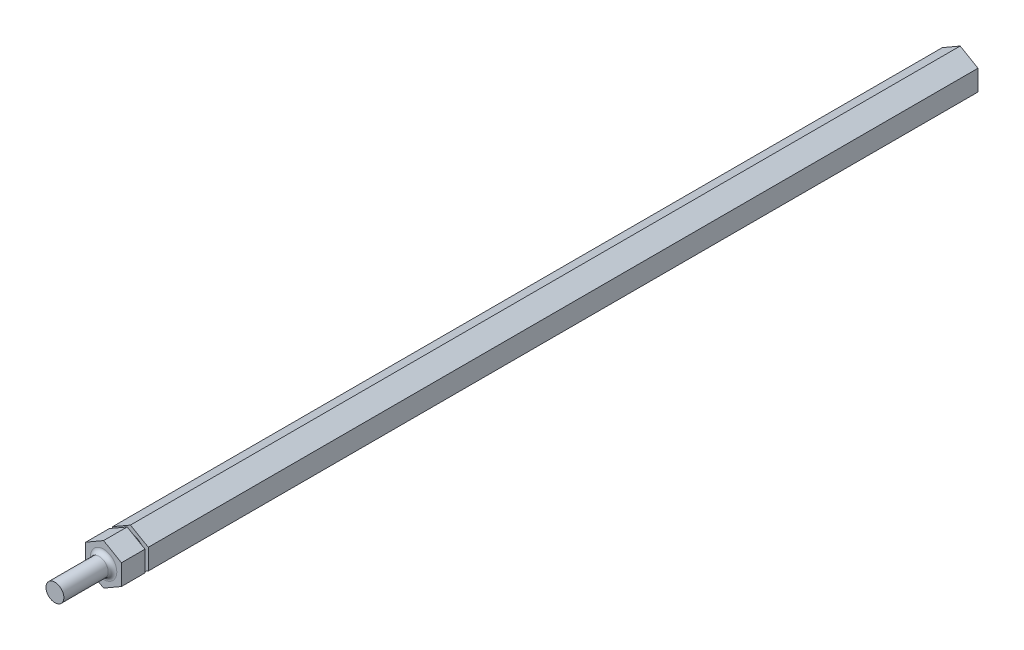
SolidWorks part; units mm, degrees
ref_plane "Front Plane" through (0, 0, 0) normal (0, 0, 1) x (1, 0, 0)
ref_plane "Top Plane" through (0, 0, 0) normal (0, 1, 0) x (1, 0, 0)
ref_plane "Right Plane" through (0, 0, 0) normal (1, 0, 0) x (0, 0, -1)
sketch "Sketch1" plane through (0, 0, 0) normal (0, 0, 1) x (1, 0, 0)
  line L1 (-6.35, 3.6662) -> (-6.35, -3.6662)
  line L2 (-6.35, -3.6662) -> (0, -7.3323)
  line L3 (0, -7.3323) -> (6.35, -3.6662)
  line L4 (6.35, -3.6662) -> (6.35, 3.6662)
  line L5 (6.35, 3.6662) -> (0, 7.3323)
  line L6 (0, 7.3323) -> (-6.35, 3.6662)
  circle A0 centre (0, 0) radius 6.35 construction
  dimension "D1" = 12.7
extrude "Boss-Extrude1" add sketch "Sketch1" along normal blind 304.8
sketch "Sketch2" plane through (0, 0, 304.8) normal (0, 0, 1) x (1, 0, 0)
  circle A0 centre (0, 0) radius 3.175
  dimension "D1" = 6.35
extrude "Boss-Extrude2" add sketch "Sketch2" along normal blind 17.3228 contours A0
fillet "Fillet1" radius 1.524 1 edges at (3.175, 0, 304.8)
sketch "Sketch3" plane through (0, 0, 0) normal (0, 1, 0) x (1, 0, 0)
  line L0 (-11.3792, -295.2496) -> (-5.0292, -295.2496)
  line L1 (-5.0292, -295.2496) -> (-5.0292, -296.418)
  line L2 (-5.0292, -296.418) -> (-11.3792, -296.418)
  line L3 (-11.3792, -296.418) -> (-11.3792, -295.2496)
  line L4 (0, -304.8) -> (-6.35, -304.8) construction
  line L5 (0, -330.0253) -> (0, -268.1786) construction
  line L6 (0, -304.8) -> (0, 0) construction
  point P6 (-5.0292, -295.8338)
  dimension "D1" = 1.1684
  dimension "D2" = 8.382
  dimension "D3" = 6.35
  dimension "D4" = 5.0292
revolve "Cut-Revolve1" cut sketch "Sketch3" angle 360 about L5
